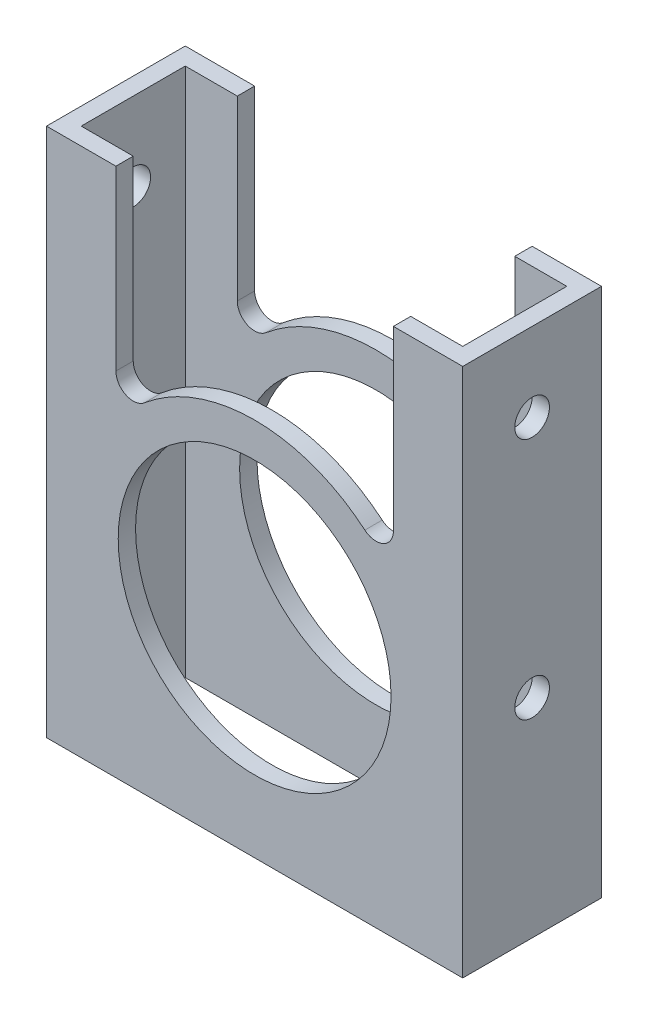
SolidWorks part; units mm, degrees
ref_plane "Front Plane" through (0, 0, 0) normal (0, 0, 1) x (1, 0, 0)
ref_plane "Top Plane" through (0, 0, 0) normal (0, 1, 0) x (1, 0, 0)
ref_plane "Right Plane" through (0, 0, 0) normal (1, 0, 0) x (0, 0, -1)
sketch "Sketch1" plane through (0, 0, 0) normal (0, 1, 0) x (1, 0, 0)
  line L1 (0, 0) -> (76.2, 0)
  line L2 (0, 0) -> (0, 25.4)
  line L3 (0, 25.4) -> (76.2, 25.4)
  line L4 (76.2, 0) -> (76.2, 25.4)
  dimension "D1" = 76.2
  dimension "D2" = 25.4
extrude "Extrude-Thin1" add sketch "Sketch1" along normal mid plane 101.6 thin thin type one direction reverse wall 3.175
sketch "Sketch2" plane through (0, 0, -25.4) normal (0, 0, -1) x (-1, 0, 0)
  line L7 (0, -50.8) -> (-76.2, 25.4) construction
  line L8 (-76.2, 50.8) -> (-76.2, -50.8) construction
  line L9 (0, 50.8) -> (0, -50.8) construction
  line L10 (-76.2, -50.8) -> (0, 25.4) construction
  circle A0 centre (-5.2832, 20.1168) radius 2.4892 construction
  circle A2 centre (-38.1, -12.7) radius 24.972
  circle A3 centre (-70.9168, -45.5168) radius 2.4892 construction
  point P14 (-2.794, 20.1168)
  point P17 (-73.406, -45.5168)
  dimension "D1" = 2.794
  dimension "D2" = 4.9784
  dimension "D3" = 49.944
  dimension "D4" = 2.794
extrude "Cut-Extrude1" cut sketch "Sketch2" against normal blind 52.578
sketch "Sketch5" plane through (0, 0, -25.4) normal (0, 0, -1) x (-1, 0, 0)
  line L0 (0, 50.8) -> (0, -50.8) construction
  line L1 (-76.2, 60.452) -> (0, 60.452)
  line L2 (-76.2, 60.452) -> (-76.2, 46.1645)
  line L3 (-76.2, 46.1645) -> (0, 46.1645)
  line L4 (0, 60.452) -> (0, 46.1645)
  line L6 (-63.5, 46.1645) -> (-12.7, 46.1645)
  line L7 (-63.5, 46.1645) -> (-63.5, 5.6278)
  line L8 (-63.5, 5.6278) -> (-12.7, 5.6278)
  line L9 (-12.7, 46.1645) -> (-12.7, 5.6278)
  line L10 (-76.2, 50.8) -> (-76.2, -50.8) construction
  circle A0 centre (-38.1, -12.7) radius 31.322
  arc A1 (-58.2795, 11.2553) -> (-63.5, 13.6836) centre (-60.325, 13.6836) cw
  arc A2 (-17.9205, 11.2553) -> (-12.7, 13.6836) centre (-15.875, 13.6836) ccw
  circle A3 centre (-38.1, -12.7) radius 24.972 construction
  point P21 (-38.1, 18.622)
  line M14 (0, -50.8) -> (0, 50.8)
  line M15 (0, 50.8) -> (-76.2, 50.8)
  line M16 (-76.2, 50.8) -> (-76.2, -50.8)
  dimension "D1" = 6.35
  dimension "D5" = 3.175
  dimension "D2" = 73.152
  dimension "D3" = 12.7
  dimension "D6" = 14.2875
extrude "Cut-Extrude2" cut sketch "Sketch5" against normal through all contours L3 M16 M14 M15 | A0 A2 L9 L3 L7 A1
sketch "Sketch6" plane through (0, 0, 0) normal (-1, 0, 0) x (0, 0, 1)
  line L0 (-12.7, 46.1645) -> (-12.7, 31.75) construction
  line L1 (0, 46.1645) -> (-25.4, 46.1645) construction
  line L2 (-25.4, -37.672) -> (-25.4, 12.272) construction
  line L3 (-25.4, 46.1645) -> (-25.4, -50.8) construction
  circle A0 centre (-12.7, 31.75) radius 3.175
  point P9 (-25.4, -12.7)
  dimension "D1" = 6.35
  dimension "D2" = 44.45
extrude "Cut-Extrude3" cut sketch "Sketch6" against normal through all
sketch "Sketch7" plane through (0, 0, 0) normal (-1, 0, 0) x (0, 0, 1)
  line L0 (-25.4, 12.272) -> (-25.4, -37.672) construction
  line L1 (-25.4, 12.272) -> (-25.4, -37.672) construction
  line L2 (-25.4, 12.272) -> (-25.4, -37.672)
  line L3 (-25.4, 12.272) -> (-25.4, -37.672)
  line L4 (-25.4, -12.7) -> (0, -12.7) construction
  line L5 (0, 46.1645) -> (0, -50.8) construction
  circle A0 centre (-12.7, -12.7) radius 3.175
  dimension "D1" = 6.35
extrude "Cut-Extrude4" cut sketch "Sketch7" against normal through all contours A0
